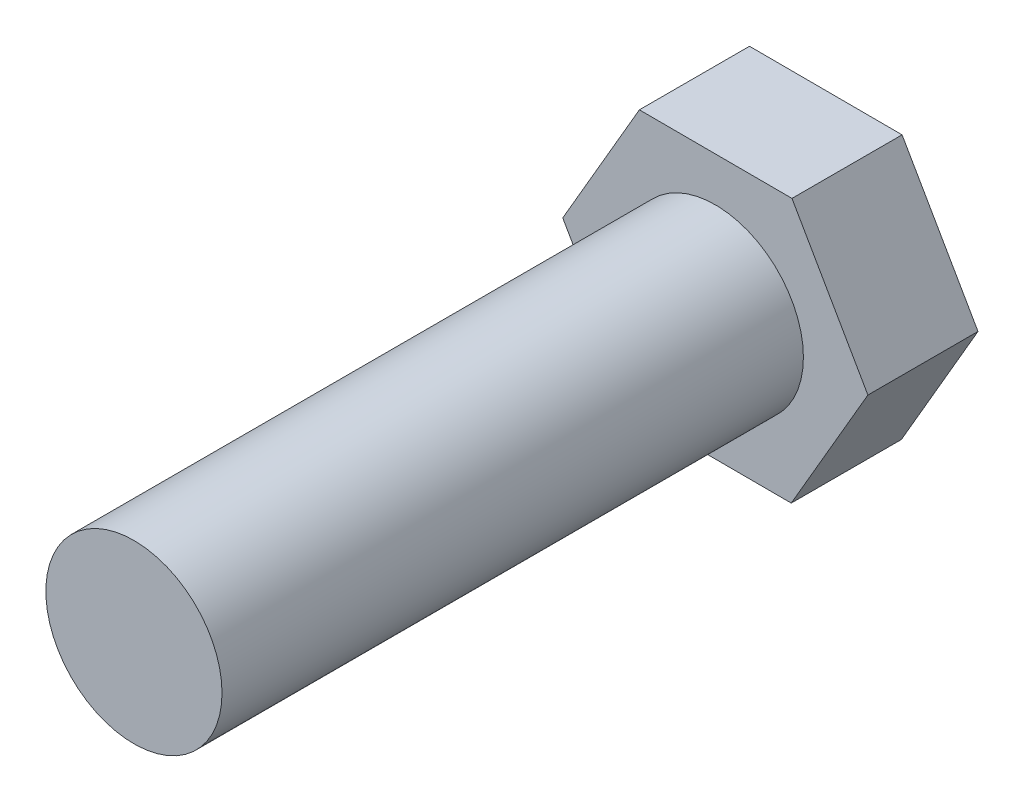
SolidWorks part; units mm, degrees
ref_plane "Front Plane" through (0, 0, 0) normal (0, 0, 1) x (1, 0, 0)
ref_plane "Top Plane" through (0, 0, 0) normal (0, 1, 0) x (1, 0, 0)
ref_plane "Right Plane" through (0, 0, 0) normal (1, 0, 0) x (0, 0, -1)
sketch "Sketch1" plane through (0, 0, 0) normal (0, 0, 1) x (1, 0, 0)
  line L1 (5.4732, -9.54) -> (10.9985, -0.0301)
  line L2 (10.9985, -0.0301) -> (5.5253, 9.5099)
  line L3 (5.5253, 9.5099) -> (-5.4732, 9.54)
  line L4 (-5.4732, 9.54) -> (-10.9985, 0.0301)
  line L5 (-10.9985, 0.0301) -> (-5.5253, -9.5099)
  line L6 (-5.5253, -9.5099) -> (5.4732, -9.54)
  circle A0 centre (0, 0) radius 9.525 construction
  dimension "D1" = 19.05
extrude "Boss-Extrude1" add sketch "Sketch1" along normal blind 7.9375
sketch "Sketch2" plane through (0, 0, 7.9375) normal (0, 0, 1) x (1, 0, 0)
  circle A0 centre (0, 0) radius 6.35
  dimension "D1" = 12.7
extrude "Boss-Extrude2" add sketch "Sketch2" along normal blind 41.91
